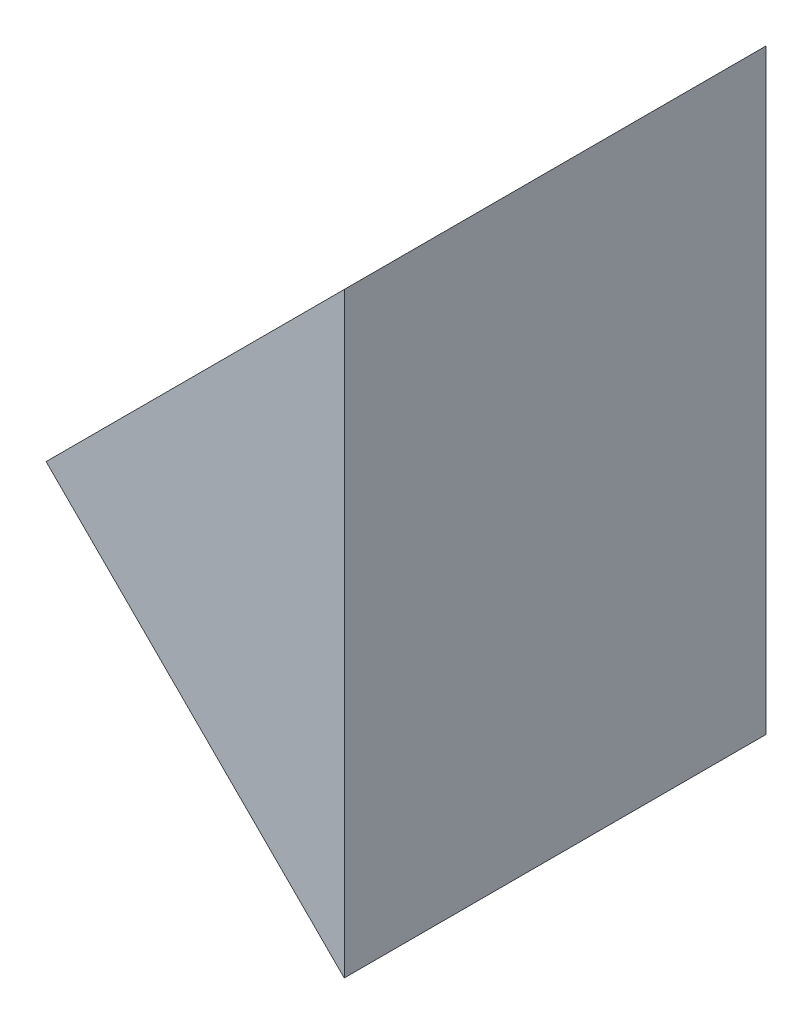
SolidWorks part; units mm, degrees
ref_plane "前视基准面" through (0, 0, 0) normal (0, 0, 1) x (1, 0, 0)
ref_plane "上视基准面" through (0, 0, 0) normal (0, 1, 0) x (1, 0, 0)
ref_plane "右视基准面" through (0, 0, 0) normal (1, 0, 0) x (0, 0, -1)
sketch "草图1" plane through (0, 0, 0) normal (0, 0, 1) x (1, 0, 0)
  line L0 (147.5305, 45.0458) -> (136.9239, 34.4392)
  line L1 (136.9239, 34.4392) -> (147.5305, 23.8326)
  line L2 (147.5305, 23.8326) -> (147.5305, 45.0458)
  dimension "D1" = 15
  dimension "D2" = 15
extrude "凸台-拉伸1" add sketch "草图1" along normal blind 15
